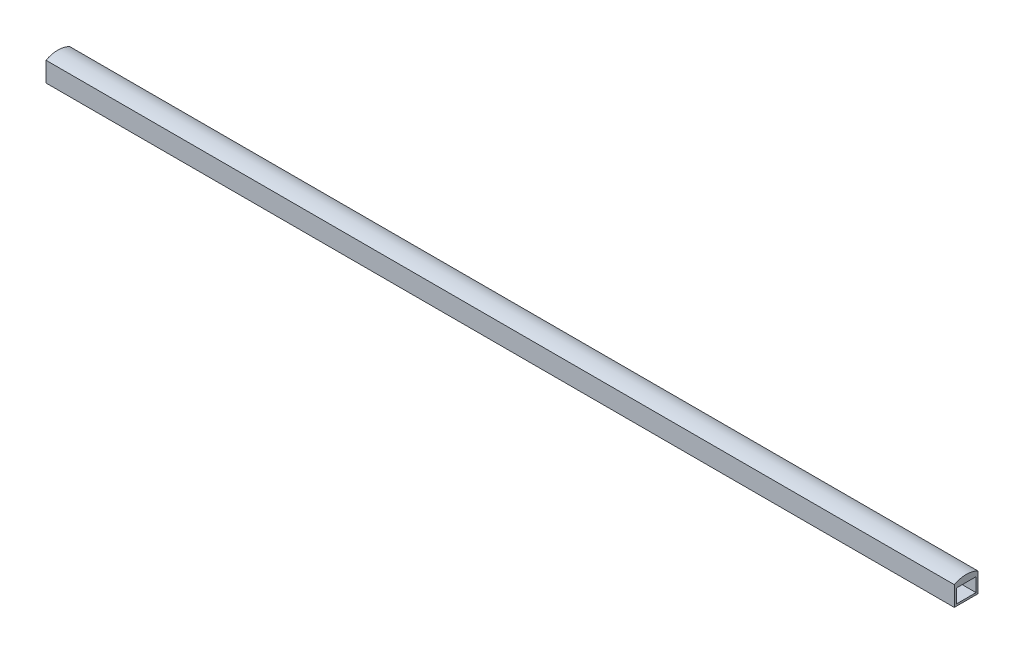
SolidWorks part; units mm, degrees
ref_plane "Front Plane" through (0, 0, 0) normal (0, 0, 1) x (1, 0, 0)
ref_plane "Top Plane" through (0, 0, 0) normal (0, 1, 0) x (1, 0, 0)
ref_plane "Right Plane" through (0, 0, 0) normal (1, 0, 0) x (0, 0, -1)
sketch "Croquis1" plane through (0, 0, 0) normal (0, 1, 0) x (1, 0, 0)
  line L0 (0, 0) -> (0, 12)
  line L1 (0, 12) -> (460, 12)
  line L2 (460, 12) -> (460, 0)
  line L3 (460, 0) -> (0, 0)
  dimension "D1" = 12
  dimension "D2" = 460
extrude "Saliente-Extruir1" add sketch "Croquis1" along normal blind 10
sketch "Croquis2" plane through (0, 0, 0) normal (-1, 0, 0) x (0, 0, 1)
  line L0 (-1, 1) -> (-1, 8)
  line L1 (-1, 1) -> (-11, 1)
  line L2 (-1, 8) -> (-11, 8)
  line L3 (-11, 1) -> (-11, 8)
  line L4 (-1, 1) -> (-11, 8) construction
  line L5 (-1, 8) -> (-11, 1) construction
  line L6 (0, 10) -> (0, 0) construction
  line L7 (-12, 0) -> (0, 0) construction
  point P1 (-6, 4.5)
  dimension "D1" = 6
  dimension "D2" = 10
  dimension "D3" = 7
  dimension "D4" = 1
extrude "Cortar-Extruir1" cut sketch "Croquis2" against normal blind 970
sketch "Croquis3" plane through (0, 0, 0) normal (-1, 0, 0) x (0, 0, 1)
  line L0 (-12, 10) -> (0, 10)
  circle A1 centre (-6, -1.5533) radius 13.0184
  line M7 (0, 10) -> (-12, 10)
extrude "Saliente-Extruir2" add sketch "Croquis3" against normal blind 460 contours A1 M7
